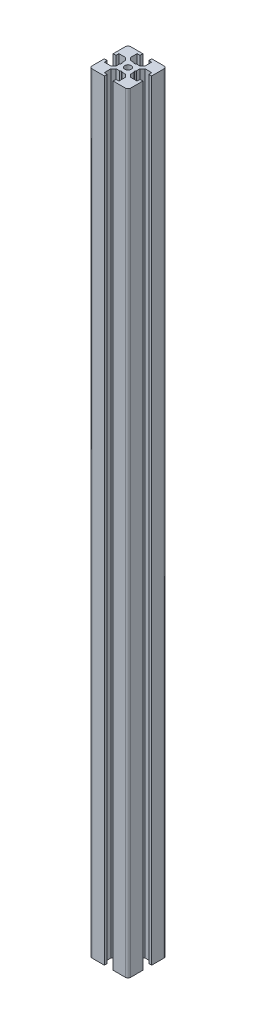
SolidWorks part; units mm, degrees
ref_plane "Front Plane" through (0, 0, 0) normal (0, 0, 1) x (1, 0, 0)
ref_plane "Top Plane" through (0, 0, 0) normal (0, 1, 0) x (1, 0, 0)
ref_plane "Right Plane" through (0, 0, 0) normal (1, 0, 0) x (0, 0, -1)
sketch "Sketch1" plane through (0, 0, 0) normal (0, 1, 0) x (1, 0, 0)
  line L0 (0, 7.5) -> (0, -7.5) construction
  line L1 (6.5, -7.5) -> (1.7, -7.5)
  line L2 (7.5, -6.5) -> (7.5, -1.7)
  line L3 (6.5, 7.5) -> (1.7, 7.5)
  line L4 (-7.5, -6.5) -> (-7.5, -1.7)
  line L5 (7.5, -7.5) -> (-7.5, 7.5) construction
  line L6 (7.5, 7.5) -> (-7.5, -7.5) construction
  line L7 (-1.7, 7.5) -> (-1.7, 6.4)
  line L8 (-1.7, 6.4) -> (-2.85, 6.4)
  line L9 (-2.85, 6.4) -> (-2.85, 3.8)
  line L10 (-1.85, 2.8) -> (-0.5196, 2.8)
  line L11 (-2.85, 3.8) -> (-1.85, 2.8)
  line L12 (0, 2.5) -> (-0.5196, 2.8)
  line L13 (-1.7, 7.5) -> (-6.5, 7.5)
  line L14 (0, 2.5) -> (0.5196, 2.8)
  line L15 (2.85, 3.8) -> (1.85, 2.8)
  line L16 (1.85, 2.8) -> (0.5196, 2.8)
  line L17 (2.85, 6.4) -> (2.85, 3.8)
  line L18 (1.7, 6.4) -> (2.85, 6.4)
  line L19 (1.7, 7.5) -> (1.7, 6.4)
  line L20 (7.5, 1.7) -> (6.4, 1.7)
  line L21 (6.4, 1.7) -> (6.4, 2.85)
  line L22 (6.4, 2.85) -> (3.8, 2.85)
  line L23 (2.8, 1.85) -> (2.8, 0.5196)
  line L24 (3.8, 2.85) -> (2.8, 1.85)
  line L25 (2.5, 0) -> (2.8, 0.5196)
  line L26 (2.5, 0) -> (2.8, -0.5196)
  line L27 (3.8, -2.85) -> (2.8, -1.85)
  line L28 (2.8, -1.85) -> (2.8, -0.5196)
  line L29 (6.4, -2.85) -> (3.8, -2.85)
  line L30 (6.4, -1.7) -> (6.4, -2.85)
  line L31 (7.5, -1.7) -> (6.4, -1.7)
  line L32 (1.7, -7.5) -> (1.7, -6.4)
  line L33 (1.7, -6.4) -> (2.85, -6.4)
  line L34 (2.85, -6.4) -> (2.85, -3.8)
  line L35 (1.85, -2.8) -> (0.5196, -2.8)
  line L36 (2.85, -3.8) -> (1.85, -2.8)
  line L37 (0, -2.5) -> (0.5196, -2.8)
  line L38 (0, -2.5) -> (-0.5196, -2.8)
  line L39 (-2.85, -3.8) -> (-1.85, -2.8)
  line L40 (-1.85, -2.8) -> (-0.5196, -2.8)
  line L41 (-2.85, -6.4) -> (-2.85, -3.8)
  line L42 (-1.7, -6.4) -> (-2.85, -6.4)
  line L43 (-1.7, -7.5) -> (-1.7, -6.4)
  line L44 (-7.5, -1.7) -> (-6.4, -1.7)
  line L45 (-6.4, -1.7) -> (-6.4, -2.85)
  line L46 (-6.4, -2.85) -> (-3.8, -2.85)
  line L47 (-2.8, -1.85) -> (-2.8, -0.5196)
  line L48 (-3.8, -2.85) -> (-2.8, -1.85)
  line L49 (-2.5, 0) -> (-2.8, -0.5196)
  line L50 (-2.5, 0) -> (-2.8, 0.5196)
  line L51 (-3.8, 2.85) -> (-2.8, 1.85)
  line L52 (-2.8, 1.85) -> (-2.8, 0.5196)
  line L53 (-6.4, 2.85) -> (-3.8, 2.85)
  line L54 (-6.4, 1.7) -> (-6.4, 2.85)
  line L55 (-7.5, 1.7) -> (-6.4, 1.7)
  line L56 (7.5, 1.7) -> (7.5, 6.5)
  line L57 (-1.7, -7.5) -> (-6.5, -7.5)
  line L58 (-7.5, 1.7) -> (-7.5, 6.5)
  circle A0 centre (0, 0) radius 1.25
  arc A1 (6.5, -7.5) -> (7.5, -6.5) centre (6.5, -6.5) ccw
  arc A2 (-6.5, -7.5) -> (-7.5, -6.5) centre (-6.5, -6.5) cw
  arc A3 (7.5, 6.5) -> (6.5, 7.5) centre (6.5, 6.5) ccw
  arc A4 (-6.5, 7.5) -> (-7.5, 6.5) centre (-6.5, 6.5) ccw
  point P0 (0, 0)
  point P12 (-2.85, 2.8)
  point P22 (2.85, 2.8)
  point P30 (2.8, 2.85)
  point P40 (2.8, -2.85)
  point P45 (2.85, -2.8)
  point P55 (-2.85, -2.8)
  point P60 (-2.8, -2.85)
  point P70 (-2.8, 2.85)
  point P71 (0, 0)
  dimension "D2" = 2.5
  dimension "D10" = 1
  dimension "D1" = 15
  dimension "D3" = 1.7
  dimension "D4" = 2.85
  dimension "D5" = 1.1
  dimension "D6" = 3.6
  dimension "D7" = 60
  dimension "D8" = 4
extrude "Boss-Extrude1" add sketch "Sketch1" along normal blind 300
